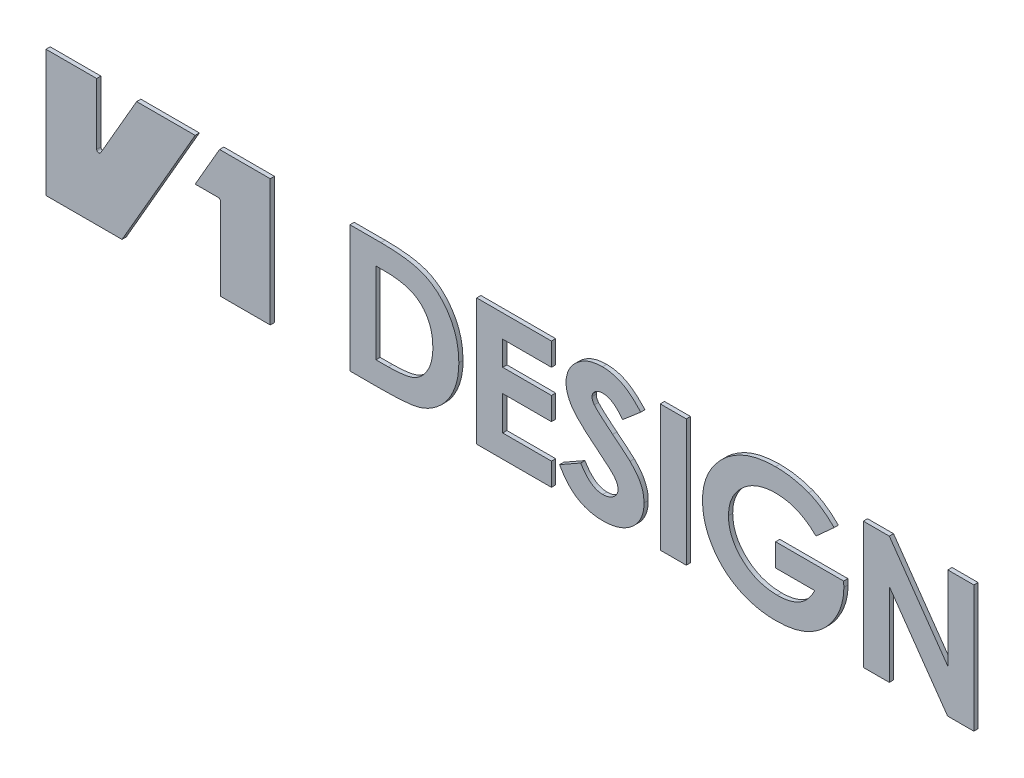
SolidWorks part; units mm, degrees
ref_plane "Front Plane" through (0, 0, 0) normal (0, 0, 1) x (1, 0, 0)
ref_plane "Top Plane" through (0, 0, 0) normal (0, 1, 0) x (1, 0, 0)
ref_plane "Right Plane" through (0, 0, 0) normal (1, 0, 0) x (0, 0, -1)
sketch "Model" plane through (0, 0, 0) normal (0, 0, 1) x (1, 0, 0)
  line L0 (53.094, 0) -> (53.094, 30)
  line L1 (41.3205, 0) -> (53.094, 0)
  line L2 (41.3205, 19.5) -> (41.3205, 0)
  line L3 (35.3205, 20) -> (40.8205, 20)
  line L4 (41.094, 30) -> (35.3205, 20)
  line L5 (53.094, 30) -> (41.094, 30)
  line L6 (0, 30) -> (0, 0)
  line L7 (12, 30) -> (0, 30)
  line L8 (12, 15.4737) -> (12, 30)
  line L9 (21.4641, 30) -> (12.933, 15.2237)
  line L10 (35.3205, 30) -> (21.4641, 30)
  line L11 (18, 0) -> (35.3205, 30)
  line L12 (0, 0) -> (18, 0)
  line L13 (193.5151, 30) -> (199.669, 30)
  line L14 (199.669, 30) -> (213.5151, 10.2584)
  line L15 (213.5151, 10.2584) -> (213.5151, 30)
  line L16 (213.5151, 30) -> (219.669, 30)
  line L17 (219.669, 30) -> (219.669, 0)
  line L18 (219.669, 0) -> (213.4731, 0)
  line L19 (213.4731, 0) -> (199.669, 19.6815)
  line L20 (199.669, 19.6815) -> (199.669, 0)
  line L21 (199.669, 0) -> (193.5151, 0)
  line L22 (193.5151, 0) -> (193.5151, 30)
  line L23 (186.6161, 25.2284) -> (182.3012, 21.3281)
  line L24 (182.0187, 10) -> (172.7459, 10)
  line L25 (172.7459, 10) -> (172.7459, 15.3846)
  line L26 (172.7459, 15.3846) -> (188.8577, 15.3846)
  line L27 (188.8577, 15.3846) -> (188.8998, 14.1046)
  line L28 (145.4382, 30) -> (151.5921, 30)
  line L29 (151.5921, 30) -> (151.5921, 0)
  line L30 (151.5921, 0) -> (145.4382, 0)
  line L31 (145.4382, 0) -> (145.4382, 30)
  line L32 (140.8228, 25.9916) -> (136.5139, 22.3077)
  line L33 (121.5921, 5.619) -> (126.6041, 8.4615)
  line L34 (101.9767, 30) -> (119.669, 30)
  line L35 (119.669, 30) -> (119.669, 24.6154)
  line L36 (108.1305, 24.6154) -> (108.1305, 18.8462)
  line L37 (119.669, 18.8462) -> (119.669, 13.4615)
  line L38 (108.1305, 13.4615) -> (108.1305, 5.3846)
  line L39 (108.1305, 5.3846) -> (119.669, 5.3846)
  line L40 (119.669, 5.3846) -> (119.669, 0)
  line L41 (119.669, 0) -> (101.9767, 0)
  line L42 (101.9767, 0) -> (101.9767, 30)
  line L43 (119.669, 24.6154) -> (108.1305, 24.6154)
  line L44 (119.669, 13.4615) -> (108.1305, 13.4615)
  line L45 (108.1305, 18.8462) -> (119.669, 18.8462)
  line L46 (78.1305, 24.6154) -> (78.1305, 5.3846)
  line L47 (71.9767, 30) -> (79.3084, 30)
  line L48 (71.9767, 0) -> (71.9767, 30)
  line L49 (80.2459, 24.6154) -> (78.1305, 24.6154)
  line L50 (79.4166, 0) -> (71.9767, 0)
  line L51 (78.1305, 5.3846) -> (81.0212, 5.3846)
  arc A0 (41.3205, 19.5) -> (40.8205, 20) centre (40.8205, 19.5) ccw
  arc A1 (12, 15.4737) -> (12.933, 15.2237) centre (12.5, 15.4737) ccw
  spline S0 degree 3 poles (182.3012, 21.3281) (181.9584, 21.6513) (181.2846, 22.2867) (180.1893, 23.1111) (179.0569, 23.8117) (177.8814, 24.3911) (176.6592, 24.8337) (175.3958, 25.1559) (174.0897, 25.3444) (173.2052, 25.3711) (172.7579, 25.3846) knots 0 0 0 0 0.132628 0.260724 0.385381 0.507275 0.629201 0.750872 0.874009 1 1 1 1
  spline S1 degree 3 poles (172.7579, 25.3846) (172.3689, 25.3752) (171.6064, 25.3569) (170.4856, 25.2164) (169.4141, 24.9812) (168.3873, 24.6598) (167.4142, 24.232) (166.4839, 23.7242) (165.6097, 23.1084) (164.7868, 22.4193) (164.039, 21.6614) (163.3856, 20.8514) (162.8303, 20.0027) (162.3726, 19.1117) (162.0278, 18.1779) (161.7707, 17.2068) (161.6179, 16.1948) (161.6007, 15.5053) (161.5921, 15.1563) knots 0 0 0 0 0.06914 0.135525 0.200412 0.263929 0.326444 0.38908 0.452005 0.5162 0.579655 0.64094 0.700891 0.759656 0.818588 0.877492 0.937975 1 1 1 1
  spline S2 degree 3 poles (161.5921, 15.1563) (161.6025, 14.7951) (161.623, 14.0833) (161.7849, 13.0383) (162.04, 12.0331) (162.4132, 11.0753) (162.8743, 10.1509) (163.4594, 9.2815) (164.1348, 8.4444) (164.9142, 7.6661) (165.7625, 6.948) (166.6782, 6.328) (167.6343, 5.7931) (168.6462, 5.3683) (169.7012, 5.0284) (170.8062, 4.7901) (171.9586, 4.6417) (172.7435, 4.6243) (173.1425, 4.6154) knots 0 0 0 0 0.06217 0.122518 0.181671 0.240417 0.299195 0.359183 0.420492 0.484156 0.548553 0.611605 0.674294 0.736892 0.800275 0.864893 0.931298 1 1 1 1
  spline S3 degree 3 poles (173.1425, 4.6154) (173.4031, 4.6176) (173.9132, 4.6219) (174.6613, 4.6928) (175.3791, 4.7953) (176.0684, 4.9265) (176.7222, 5.1198) (177.3486, 5.3388) (177.9444, 5.6025) (178.5071, 5.9134) (179.0449, 6.2604) (179.5496, 6.6592) (180.0276, 7.1032) (180.4853, 7.588) (180.9106, 8.1245) (181.3087, 8.7057) (181.6831, 9.3314) (181.9054, 9.7741) (182.0187, 10) knots 0 0 0 0 0.070732 0.138447 0.203834 0.267627 0.328746 0.38879 0.44772 0.505415 0.563199 0.621307 0.679817 0.740234 0.802163 0.865533 0.931393 1 1 1 1
  spline S4 degree 3 poles (188.8998, 14.1046) (188.8924, 13.7758) (188.8777, 13.1186) (188.7721, 12.1408) (188.6059, 11.1741) (188.3622, 10.2233) (188.0566, 9.2823) (187.6767, 8.3574) (187.2277, 7.4459) (186.7221, 6.5516) (186.1603, 5.6902) (185.5506, 4.8765) (184.9027, 4.1115) (184.21, 3.4028) (183.4812, 2.7441) (182.7103, 2.1412) (181.8958, 1.5964) (181.049, 1.0928) (180.1579, 0.6555) (179.2276, 0.276) (178.2622, -0.0477) (177.2588, -0.3136) (176.2168, -0.518) (175.1367, -0.6578) (174.0196, -0.7533) (173.2629, -0.7639) (172.8781, -0.7692) knots 0 0 0 0 0.040453 0.080851 0.12089 0.161066 0.201523 0.242538 0.283989 0.326488 0.368878 0.410438 0.451532 0.492148 0.532292 0.572332 0.612464 0.652795 0.693474 0.734489 0.776348 0.81868 0.862141 0.906903 0.952656 1 1 1 1
  spline S5 degree 3 poles (172.8781, -0.7692) (172.4653, -0.764) (171.6505, -0.7537) (170.4464, -0.6554) (169.2771, -0.4922) (168.1413, -0.2708) (167.0368, 0.0115) (165.9662, 0.3592) (164.9317, 0.7759) (163.9331, 1.2496) (162.979, 1.783) (162.0742, 2.3745) (161.219, 3.0189) (160.4118, 3.7156) (159.661, 4.4689) (158.9582, 5.2724) (158.3106, 6.134) (157.7115, 7.0415) (157.1787, 7.9881) (156.7164, 8.9591) (156.3146, 9.9439) (156, 10.9527) (155.7416, 11.9747) (155.5729, 13.0185) (155.4581, 14.078) (155.4449, 14.7914) (155.4382, 15.1502) knots 0 0 0 0 0.046942 0.09265 0.137271 0.181144 0.224186 0.266834 0.309053 0.350933 0.392443 0.433261 0.473766 0.514141 0.554413 0.594616 0.63544 0.676889 0.7182 0.758856 0.799129 0.839043 0.878935 0.918896 0.959199 1 1 1 1
  spline S6 degree 3 poles (155.4382, 15.1502) (155.4506, 15.6397) (155.475, 16.6067) (155.6797, 18.0318) (156.0097, 19.4087) (156.4729, 20.7367) (157.0761, 22.0112) (157.7967, 23.2432) (158.6621, 24.4227) (159.3256, 25.152) (159.663, 25.5228) knots 0 0 0 0 0.127753 0.252394 0.375069 0.496985 0.618892 0.742685 0.869166 1 1 1 1
  spline S7 degree 3 poles (159.663, 25.5228) (159.873, 25.7376) (160.2903, 26.1644) (160.9542, 26.7582) (161.6399, 27.3151) (162.3542, 27.8209) (163.0862, 28.2954) (163.8423, 28.7273) (164.6247, 29.1185) (165.4313, 29.4674) (166.2602, 29.7735) (167.1132, 30.0378) (167.9881, 30.2694) (168.8907, 30.4442) (169.8121, 30.5925) (170.7592, 30.6906) (171.7292, 30.7624) (172.3852, 30.7669) (172.7159, 30.7692) knots 0 0 0 0 0.062204 0.123613 0.1844 0.245082 0.304819 0.365037 0.425348 0.485937 0.546985 0.608276 0.670877 0.734353 0.798617 0.864145 0.931522 1 1 1 1
  spline S8 degree 3 poles (172.7159, 30.7692) (173.0625, 30.7642) (173.7525, 30.7543) (174.777, 30.6861) (175.7861, 30.5802) (176.7761, 30.4216) (177.7519, 30.2263) (178.709, 29.9757) (179.6513, 29.6924) (180.265, 29.4644) (180.5704, 29.351) knots 0 0 0 0 0.129556 0.257844 0.383597 0.508653 0.63243 0.755363 0.878276 1 1 1 1
  spline S9 degree 3 poles (180.5704, 29.351) (180.8284, 29.2463) (181.3521, 29.0338) (182.1161, 28.6464) (182.8787, 28.2088) (183.6424, 27.7272) (184.3911, 27.1733) (185.1445, 26.5804) (185.8909, 25.9308) (186.3718, 25.465) (186.6161, 25.2284) knots 0 0 0 0 0.11331 0.230033 0.348397 0.471256 0.597365 0.72742 0.861541 1 1 1 1
  spline S10 degree 3 poles (136.5139, 22.3077) (136.3272, 22.551) (135.9685, 23.0182) (135.3956, 23.645) (134.8244, 24.1805) (134.2454, 24.6181) (133.6605, 24.9588) (133.0729, 25.2025) (132.4813, 25.3566) (132.0837, 25.3753) (131.8865, 25.3846) knots 0 0 0 0 0.159665 0.306609 0.441699 0.566883 0.683727 0.793184 0.897426 1 1 1 1
  spline S11 degree 3 poles (129.2844, 23.4195) (129.2924, 23.2947) (129.3086, 23.0437) (129.4066, 22.6717) (129.5785, 22.3142) (129.7337, 22.0953) (129.8132, 21.9832) knots 0 0 0 0 0.240347 0.48368 0.735669 1 1 1 1
  spline S12 degree 3 poles (129.8132, 21.9832) (129.8884, 21.8962) (130.061, 21.6967) (130.3814, 21.3773) (130.7864, 20.9887) (131.2887, 20.5396) (131.8757, 20.0224) (132.5599, 19.4451) (133.3301, 18.7988) (133.8773, 18.3489) (134.1642, 18.113) knots 0 0 0 0 0.059168 0.135724 0.232716 0.348057 0.482492 0.635372 0.80884 1 1 1 1
  spline S13 degree 3 poles (134.1642, 18.113) (134.4322, 17.8942) (134.9419, 17.4781) (135.6712, 16.8947) (136.3059, 16.3602) (136.8676, 15.9035) (137.3346, 15.496) (137.7276, 15.1625) (138.0336, 14.8872) (138.2069, 14.7219) (138.2808, 14.6514) knots 0 0 0 0 0.192959 0.366899 0.520799 0.655676 0.770541 0.866383 0.943105 1 1 1 1
  spline S14 degree 3 poles (138.2808, 14.6514) (138.5642, 14.3655) (139.1071, 13.8176) (139.8091, 12.9591) (140.3993, 12.1319) (140.8443, 11.2991) (141.1796, 10.4619) (141.4265, 9.5993) (141.5628, 8.6963) (141.5822, 8.0814) (141.5921, 7.7704) knots 0 0 0 0 0.153397 0.293911 0.422292 0.540171 0.652913 0.765578 0.88147 1 1 1 1
  spline S15 degree 3 poles (141.5921, 7.7704) (141.5844, 7.4675) (141.5693, 6.8729) (141.4387, 6.0009) (141.2308, 5.1703) (140.9343, 4.3787) (140.5437, 3.6334) (140.0842, 2.9171) (139.5211, 2.2574) (138.8957, 1.6309) (138.1933, 1.0717) (137.4398, 0.5733) (136.6307, 0.159) (135.7689, -0.1801) (134.8566, -0.4409) (133.8945, -0.6351) (132.881, -0.7509) (132.1873, -0.763) (131.8325, -0.7692) knots 0 0 0 0 0.062485 0.12264 0.181491 0.238919 0.296601 0.354845 0.414122 0.475212 0.537252 0.599048 0.661352 0.724449 0.789861 0.856904 0.926792 1 1 1 1
  spline S16 degree 3 poles (131.8325, -0.7692) (131.5538, -0.7647) (131.0037, -0.7558) (130.1928, -0.682) (129.4097, -0.563) (128.6548, -0.394) (127.9258, -0.1774) (127.2222, 0.0862) (126.5472, 0.3996) (125.8995, 0.7621) (125.279, 1.1786) (124.6823, 1.6487) (124.1108, 2.1758) (123.5548, 2.7524) (123.0301, 3.3912) (122.5208, 4.0788) (122.0413, 4.826) (121.7438, 5.3511) (121.5921, 5.619) knots 0 0 0 0 0.065469 0.129278 0.191202 0.251511 0.310946 0.369796 0.427932 0.485687 0.544056 0.603393 0.664041 0.726642 0.791503 0.858171 0.927646 1 1 1 1
  spline S17 degree 3 poles (126.6041, 8.4615) (126.7909, 8.1574) (127.1499, 7.5731) (127.7539, 6.79) (128.3725, 6.1221) (129.0127, 5.5724) (129.6791, 5.144) (130.3705, 4.8407) (131.0831, 4.6499) (131.5669, 4.6269) (131.8084, 4.6154) knots 0 0 0 0 0.157892 0.303304 0.436908 0.560192 0.675789 0.786154 0.893241 1 1 1 1
  spline S18 degree 3 poles (131.8084, 4.6154) (132.0558, 4.6249) (132.5363, 4.6434) (133.2227, 4.8114) (133.8518, 5.0758) (134.3949, 5.4549) (134.8524, 5.8927) (135.1939, 6.3775) (135.3996, 6.9076) (135.4253, 7.2739) (135.4382, 7.4579) knots 0 0 0 0 0.145479 0.282526 0.413563 0.545093 0.67022 0.784738 0.891875 1 1 1 1
  spline S19 degree 3 poles (131.1954, 12.6322) (130.7874, 12.955) (130.0056, 13.5735) (128.9027, 14.4905) (127.9102, 15.3492) (127.0269, 16.1492) (126.2622, 16.8977) (125.6025, 17.5797) (125.0595, 18.209) (124.4967, 18.9586) (123.9537, 19.8665) (123.4857, 20.9638) (123.1818, 22.061) (123.1474, 22.7986) (123.1305, 23.1611) knots 0 0 0 0 0.113807 0.218052 0.313729 0.400891 0.47867 0.547784 0.608384 0.660354 0.752714 0.838907 0.920851 1 1 1 1
  spline S20 degree 3 poles (123.1305, 23.1611) (123.1361, 23.418) (123.147, 23.9249) (123.2759, 24.6692) (123.4645, 25.3878) (123.7376, 26.0774) (124.0904, 26.7371) (124.5185, 27.3702) (125.0273, 27.973) (125.6071, 28.5402) (126.245, 29.0559) (126.9202, 29.5201) (127.64, 29.903) (128.3913, 30.2231) (129.18, 30.472) (130.0053, 30.6445) (130.8683, 30.7479) (131.4556, 30.762) (131.7543, 30.7692) knots 0 0 0 0 0.060195 0.118734 0.176621 0.234194 0.292196 0.351738 0.413088 0.476868 0.54165 0.605232 0.668705 0.732485 0.796518 0.862301 0.929949 1 1 1 1
  spline S21 degree 3 poles (131.7543, 30.7692) (132.1418, 30.7563) (132.9114, 30.7307) (134.0485, 30.5307) (135.1577, 30.2111) (136.0568, 29.8347) (136.7696, 29.4575) (137.3213, 29.1229) (137.8785, 28.7274) (138.4539, 28.2915) (139.0265, 27.7857) (139.6238, 27.2431) (140.2247, 26.6389) (140.6199, 26.2112) (140.8228, 25.9916) knots 0 0 0 0 0.109693 0.217905 0.326013 0.436139 0.49325 0.554365 0.618748 0.686732 0.758742 0.835045 0.915292 1 1 1 1
  spline S22 degree 3 poles (131.8865, 25.3846) (131.7036, 25.3788) (131.3518, 25.3677) (130.849, 25.2504) (130.3987, 25.0576) (130.0091, 24.7938) (129.6956, 24.4851) (129.4518, 24.1552) (129.3163, 23.7918) (129.2949, 23.5426) (129.2844, 23.4195) knots 0 0 0 0 0.152185 0.292647 0.427185 0.558167 0.68207 0.792258 0.897335 1 1 1 1
  spline S23 degree 3 poles (135.4382, 7.4579) (135.4292, 7.6293) (135.4108, 7.9786) (135.2479, 8.4959) (134.998, 9.0113) (134.71, 9.4352) (134.4169, 9.7928) (134.1259, 10.0939) (133.7852, 10.4386) (133.3792, 10.8101) (132.9164, 11.2164) (132.4005, 11.6652) (131.8157, 12.135) (131.4078, 12.462) (131.1954, 12.6322) knots 0 0 0 0 0.074367 0.151543 0.233745 0.322891 0.373637 0.434642 0.504858 0.584373 0.673854 0.77268 0.881649 1 1 1 1
  spline S24 degree 3 poles (88.6774, 22.2115) (88.446, 22.4066) (87.9743, 22.8042) (87.1548, 23.2853) (86.2484, 23.7045) (85.2367, 24.0361) (84.1294, 24.3004) (82.921, 24.4811) (81.6164, 24.5983) (80.7129, 24.6096) (80.2459, 24.6154) knots 0 0 0 0 0.101171 0.206175 0.316899 0.43502 0.561892 0.697616 0.843696 1 1 1 1
  spline S25 degree 3 poles (97.7459, 14.5793) (97.7314, 14.0136) (97.7028, 12.8991) (97.4618, 11.264) (97.0727, 9.6964) (96.5236, 8.2107) (95.851, 6.8146) (95.0405, 5.5409) (94.1158, 4.3874) (93.0774, 3.3713) (91.9603, 2.4895) (90.7908, 1.743) (89.5691, 1.1488) (88.4944, 0.7769) (87.5616, 0.5406) (86.7426, 0.4052) (85.8091, 0.2764) (84.7561, 0.1799) (83.5864, 0.0923) (82.2995, 0.0449) (80.8972, 0.0054) (79.9234, 0.0019) (79.4166, 0) knots 0 0 0 0 0.062998 0.124097 0.183687 0.242639 0.300227 0.356006 0.410445 0.464571 0.517477 0.568738 0.618841 0.668455 0.695138 0.725957 0.760863 0.800099 0.843727 0.891526 0.943539 1 1 1 1
  spline S26 degree 3 poles (91.5921, 14.6755) (91.5822, 15.0685) (91.5629, 15.8346) (91.4321, 16.9519) (91.2035, 18.0024) (90.8858, 18.9857) (90.4785, 19.9026) (89.9636, 20.7401) (89.3805, 21.5281) (88.9124, 21.9831) (88.6774, 22.2115) knots 0 0 0 0 0.141599 0.276081 0.404642 0.528366 0.647907 0.765142 0.882083 1 1 1 1
  spline S27 degree 3 poles (79.3084, 30) (79.8794, 29.9962) (80.986, 29.9889) (82.5875, 29.9091) (84.077, 29.7845) (85.4517, 29.6151) (86.714, 29.3877) (87.8608, 29.1086) (88.8955, 28.7782) (89.8304, 28.3985) (90.6833, 27.948) (91.4932, 27.4495) (92.2618, 26.8834) (92.9933, 26.2549) (93.6854, 25.561) (94.3403, 24.804) (94.9529, 23.9822) (95.5302, 23.1085) (96.0514, 22.182) (96.503, 21.2088) (96.8889, 20.1993) (97.2005, 19.1479) (97.4479, 18.0602) (97.6209, 16.9336) (97.7245, 15.7692) (97.7387, 14.9802) (97.7459, 14.5793) knots 0 0 0 0 0.062253 0.120638 0.17478 0.225196 0.271592 0.314553 0.353786 0.389925 0.424409 0.458836 0.493521 0.528369 0.563891 0.600279 0.637409 0.675573 0.714394 0.753187 0.792452 0.832117 0.872651 0.913982 0.956298 1 1 1 1
  spline S28 degree 3 poles (81.0212, 5.3846) (81.3658, 5.3853) (82.0295, 5.3865) (82.9868, 5.4424) (83.8721, 5.499) (84.6831, 5.6063) (85.4257, 5.7245) (86.0895, 5.8916) (86.6866, 6.0644) (87.211, 6.2871) (87.6913, 6.5386) (88.1409, 6.8273) (88.571, 7.1547) (88.9789, 7.5188) (89.3577, 7.9271) (89.7216, 8.3653) (90.0571, 8.8501) (90.3734, 9.3691) (90.666, 9.922) (90.9078, 10.5117) (91.121, 11.1291) (91.2952, 11.7774) (91.4255, 12.4588) (91.5211, 13.1709) (91.5836, 13.9131) (91.5892, 14.4189) (91.5921, 14.6755) knots 0 0 0 0 0.063486 0.122244 0.176651 0.22687 0.272924 0.315087 0.352914 0.387323 0.419847 0.452711 0.485634 0.51935 0.553293 0.588169 0.624211 0.66181 0.700109 0.739317 0.779118 0.820391 0.86288 0.90683 0.952745 1 1 1 1
extrude "Boss-Extrude1" add sketch "Model" along normal blind 1
